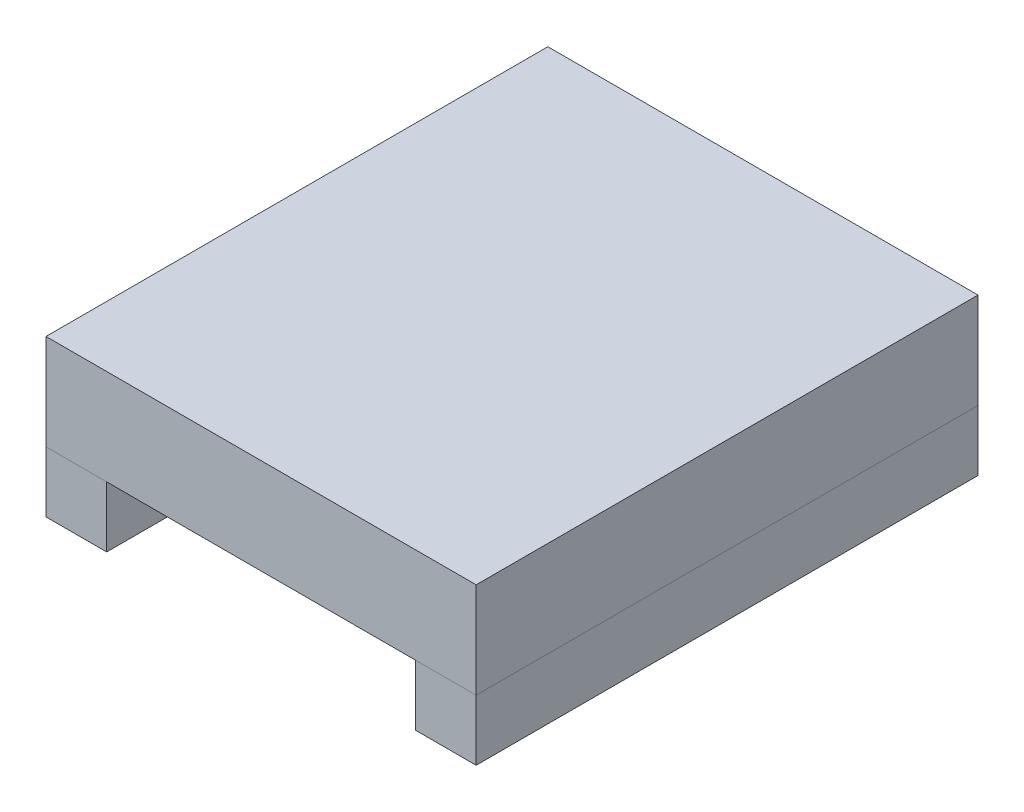
SolidWorks part; units mm, degrees
ref_plane "Спереди" through (0, 0, 0) normal (0, 0, 1) x (1, 0, 0)
ref_plane "Сверху" through (0, 0, 0) normal (0, 1, 0) x (1, 0, 0)
ref_plane "Справа" through (0, 0, 0) normal (1, 0, 0) x (0, 0, -1)
sketch "Эскиз1" plane through (0, 0, 0) normal (0, 1, 0) x (1, 0, 0)
  line L1 (-9, -10.5) -> (9, -10.5)
  line L2 (-9, -10.5) -> (-9, 10.5)
  line L3 (-9, 10.5) -> (9, 10.5)
  line L4 (9, -10.5) -> (9, 10.5)
  line L5 (-9, -10.5) -> (9, 10.5) construction
  line L6 (-9, 10.5) -> (9, -10.5) construction
  point P0 (0, 0)
  dimension "D1" = 18
  dimension "D2" = 21
extrude "Бобышка-Вытянуть1" add sketch "Эскиз1" along normal blind 4
sketch "Эскиз2" plane through (0, 0, 0) normal (0, -1, 0) x (1, 0, 0)
  line L0 (0, 10.5) -> (0, -10.5) construction
  line L1 (-9, 10.5) -> (9, 10.5) construction
  line L2 (9, -10.5) -> (-9, -10.5) construction
  line L3 (6.46, 10.5) -> (6.46, -10.5)
  line L4 (-9, 10.5) -> (-6.46, 10.5)
  line L5 (-9, 10.5) -> (-9, -10.5)
  line L6 (-9, -10.5) -> (-6.46, -10.5)
  line L7 (-6.46, 10.5) -> (-6.46, -10.5)
  line L8 (9, -10.5) -> (6.46, -10.5)
  line L9 (9, 10.5) -> (9, -10.5)
  line L10 (9, 10.5) -> (6.46, 10.5)
  dimension "D1" = 2.54
extrude "Бобышка-Вытянуть2" add sketch "Эскиз2" along normal blind 2.54 separate body
